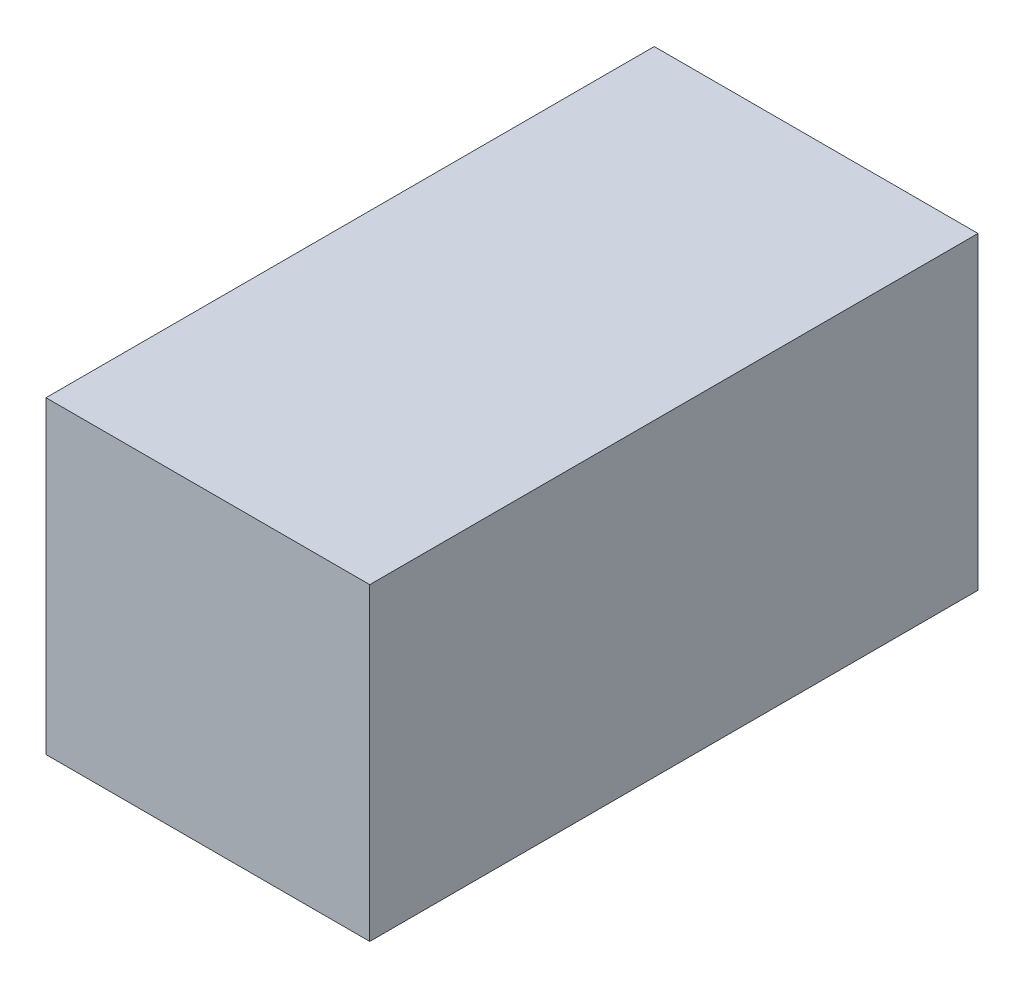
SolidWorks part; units mm, degrees
ref_plane "Plano frontal" through (0, 0, 0) normal (0, 0, 1) x (1, 0, 0)
ref_plane "Plano superior" through (0, 0, 0) normal (0, 1, 0) x (1, 0, 0)
ref_plane "Plano direito" through (0, 0, 0) normal (1, 0, 0) x (0, 0, -1)
sketch "Sketch1" plane through (0, 0, 38871.7002) normal (0, 0, 1) x (1, 0, 0)
  line L1 (-19209.8351, -7112.9352) -> (-18549.8351, -7112.9352)
  line L2 (-19209.8351, -7112.9352) -> (-19209.8351, -7742.9352)
  line L3 (-19209.8351, -7742.9352) -> (-18549.8351, -7742.9352)
  line L4 (-18549.8351, -7112.9352) -> (-18549.8351, -7742.9352)
  point P4 (-18549.8351, -7742.9352)
  dimension "D1" = 660
  dimension "D2" = 630
extrude "Boss-Extrude1" add sketch "Sketch1" along normal blind 1240 from offset 120
